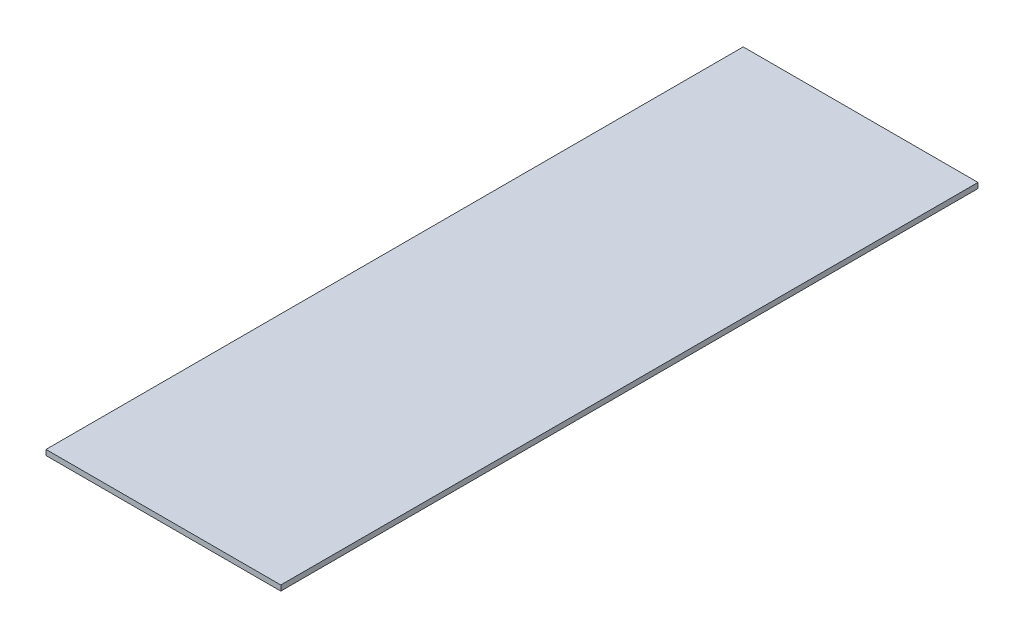
SolidWorks part; units mm, degrees
ref_plane "Front Plane" through (0, 0, 0) normal (0, 0, 1) x (1, 0, 0)
ref_plane "Top Plane" through (0, 0, 0) normal (0, 1, 0) x (1, 0, 0)
ref_plane "Right Plane" through (0, 0, 0) normal (1, 0, 0) x (0, 0, -1)
sketch "Sketch1" plane through (0, 0, 0) normal (0, 0, 1) x (1, 0, 0)
  line L1 (0, 0) -> (1676.4, 0)
  line L2 (0, 0) -> (0, 38.1)
  line L3 (0, 38.1) -> (1676.4, 38.1)
  line L4 (1676.4, 0) -> (1676.4, 38.1)
  dimension "D1" = 1676.4
  dimension "D2" = 38.1
extrude "Boss-Extrude1" add sketch "Sketch1" along normal blind 4978.4
